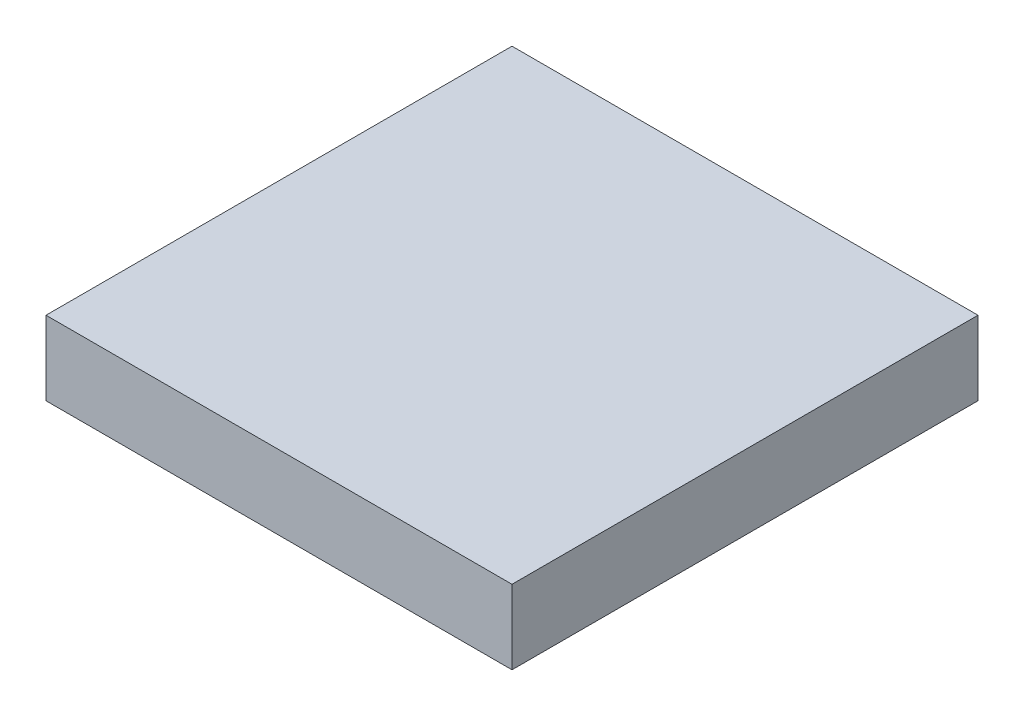
SolidWorks part; units mm, degrees
ref_plane "Front Plane" through (0, 0, 0) normal (0, 0, 1) x (1, 0, 0)
ref_plane "Top Plane" through (0, 0, 0) normal (0, 1, 0) x (1, 0, 0)
ref_plane "Right Plane" through (0, 0, 0) normal (1, 0, 0) x (0, 0, -1)
sketch "Sketch3" plane through (0, 0, 0) normal (0, 1, 0) x (1, 0, 0)
  line L1 (0, 0) -> (10, 0)
  line L2 (0, 0) -> (0, 10)
  line L3 (0, 10) -> (10, 10)
  line L4 (10, 0) -> (10, 10)
  dimension "D1" = 10
  dimension "D2" = 10
extrude "Boss-Extrude1" add sketch "Sketch3" along normal blind 1.59
sketch "Sketch7" plane through (0, 1.59, 0) normal (0, 1, 0) x (1, 0, 0)
  line L0 (0, 5) -> (10, 5)
  line L1 (0, 10) -> (0, 0) construction
  line L3 (5, 5) -> (5, 0)
  line L4 (0, 0) -> (10, 0) construction
  line L5 (10, 0) -> (10, 10) construction
  line L6 (0, 10) -> (0, 0) construction
  line L7 (0, 0) -> (10, 0) construction
  line L8 (10, 10) -> (0, 10) construction
  line L9 (8.5, 1.5) -> (1.5, 1.5) construction
  circle A0 centre (1.5, 1.5) radius 0.35
  circle A1 centre (5, 8.5) radius 0.35
  circle A2 centre (8.5, 1.5) radius 0.35
  point P2 (5, 1.5)
  point P4 (0, 0)
  point P6 (0, 0)
  point P14 (0, 5)
  point P23 (5, 0)
  dimension "D5" = 0.7
  dimension "D1" = 1.5
  dimension "D2" = 1.5
  dimension "D3" = 1.5
